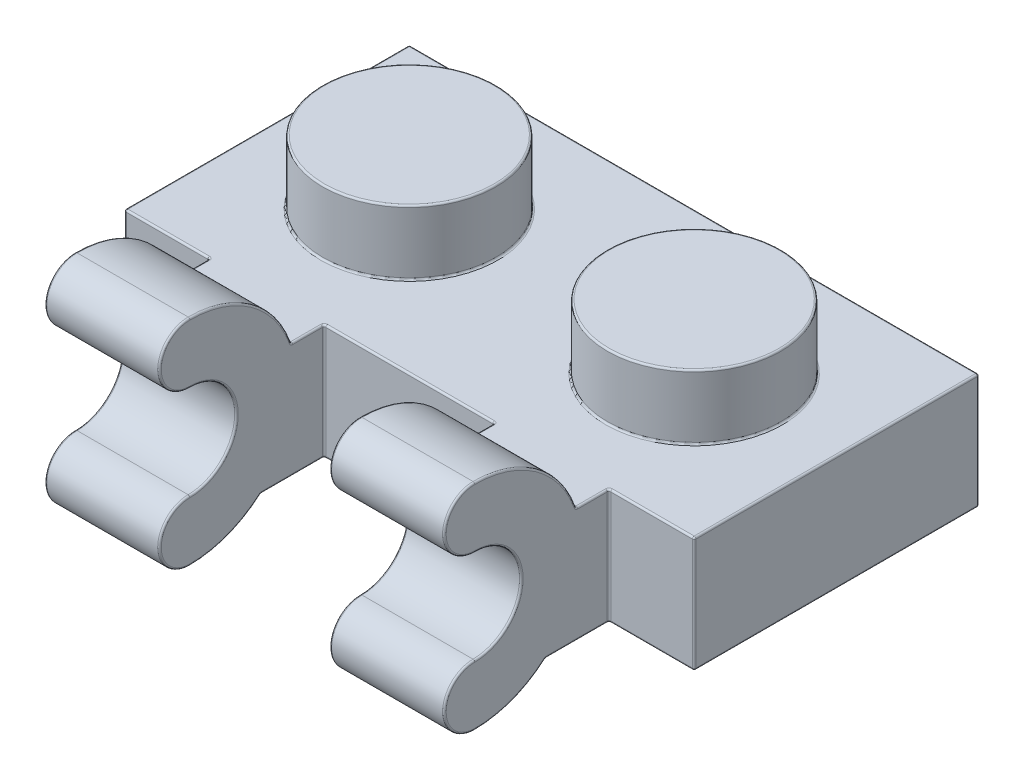
SolidWorks part; units mm, degrees
ref_plane "Front Plane" through (0, 0, 0) normal (0, 0, 1) x (1, 0, 0)
ref_plane "Top Plane" through (0, 0, 0) normal (0, 1, 0) x (1, 0, 0)
ref_plane "Right Plane" through (0, 0, 0) normal (1, 0, 0) x (0, 0, -1)
sketch "Sketch1" plane through (0, 0, 0) normal (0, 1, 0) x (1, 0, 0)
  line L1 (-3.98, 3.98) -> (3.98, 3.98)
  line L2 (-3.98, 3.98) -> (-3.98, -3.98)
  line L3 (-3.98, -3.98) -> (3.98, -3.98)
  line L4 (3.98, 3.98) -> (3.98, -3.98)
  line L5 (-3.98, 3.98) -> (3.98, -3.98) construction
  line L6 (-3.98, -3.98) -> (3.98, 3.98) construction
  point P0 (0, 0)
  dimension "D1" = 7.96
extrude "Extrude1" add sketch "Sketch1" along normal blind 3.22
sketch "Sketch2" plane through (0, 3.22, 0) normal (0, 1, 0) x (1, 0, 0)
  circle A0 centre (0, 0) radius 2.425
  dimension "D1" = 4.85
extrude "Extrude2" add sketch "Sketch2" along normal blind 1.8
pattern_linear "LPattern1" count 2 spacing 7.96 along (1, 0, 0) of "Extrude2", "Extrude1"
shell "Shell1" thickness 1.55
sketch "Sketch4" plane through (0, 1.67, 0) normal (0, -1, 0) x (1, 0, 0)
  line L0 (10.39, 2.43) -> (10.39, -2.43) construction
  line L1 (-2.43, 2.43) -> (10.39, 2.43) construction
  line L2 (-2.43, -2.43) -> (-2.43, 2.43) construction
  line L3 (10.39, -2.43) -> (-2.43, -2.43) construction
  line L4 (10.39, 2.43) -> (10.39, -2.43)
  line L5 (-2.43, 2.43) -> (10.39, 2.43)
  line L6 (-2.43, -2.43) -> (-2.43, 2.43)
  line L7 (10.39, -2.43) -> (-2.43, -2.43)
extrude "Extrude3" cut sketch "Sketch4" against normal blind 0.14
sketch "Sketch5" plane through (0, 1.81, 0) normal (0, -1, 0) x (1, 0, 0)
  line L0 (10.39, 2.43) -> (-2.43, 2.43) construction
  circle A0 centre (3.98, 0) radius 1.5
  circle A1 centre (3.98, 0) radius 0.64
  point P5 (3.98, 2.43)
  dimension "D1" = 3
  dimension "D2" = 0.86
extrude "Extrude4" add sketch "Sketch5" along normal up to surface (1.81 mm away) up to face at (3.98, 0, 0)
sketch "Sketch6" plane through (11.94, 0, 0) normal (1, 0, 0) x (0, 0, -1)
  line L0 (-3.98, 0) -> (-5.7457, 0)
  line L2 (-3.98, 3.22) -> (-3.98, 0) construction
  line L5 (-3.98, 0) -> (3.98, 0) construction
  line L7 (-3.98, 3.22) -> (-4.8911, 3.22)
  line L8 (-3.98, 3.22) -> (-3.98, 0)
  arc A0 (-4.8911, 3.22) -> (-7.73, 5.25) centre (-7.73, 2.25) ccw
  arc A1 (-7.73, 0.95) -> (-7.73, 3.55) centre (-7.73, 2.25) ccw
  arc A2 (-7.73, -0.75) -> (-5.7457, 0) centre (-7.73, 2.25) ccw
  arc A3 (-7.73, 0.95) -> (-7.73, -0.75) centre (-7.73, 0.1) ccw
  arc A4 (-7.73, 5.25) -> (-7.73, 3.55) centre (-7.73, 4.4) ccw
  dimension "D1" = 6
  dimension "D2" = 1.7
  dimension "D3" = 3.75
  dimension "D4" = 2.25
sketch "Sketch7" plane through (0, 0, 0) normal (1, 0, 0) x (0, 0, -1)
  line L0 (-3.98, 3.22) -> (-3.98, 0) construction
  line L1 (-3.98, 3.22) -> (-4.8911, 3.22) construction
  line L2 (-3.98, 0) -> (-5.7457, 0) construction
  line L3 (-3.98, 3.22) -> (-3.98, 0)
  line L4 (-3.98, 3.22) -> (-4.8911, 3.22)
  line L5 (-3.98, 0) -> (-5.7457, 0)
  arc A0 (-4.8911, 3.22) -> (-7.73, 5.25) centre (-7.73, 2.25) ccw construction
  arc A1 (-7.73, 5.25) -> (-7.73, 3.55) centre (-7.73, 4.4) ccw construction
  arc A2 (-7.73, 0.95) -> (-7.73, 3.55) centre (-7.73, 2.25) ccw construction
  arc A3 (-7.73, 0.95) -> (-7.73, -0.75) centre (-7.73, 0.1) ccw construction
  arc A4 (-7.73, -0.75) -> (-5.7457, 0) centre (-7.73, 2.25) ccw construction
  arc A5 (-4.8911, 3.22) -> (-7.73, 5.25) centre (-7.73, 2.25) ccw
  arc A6 (-7.73, 5.25) -> (-7.73, 3.55) centre (-7.73, 4.4) ccw
  arc A7 (-7.73, 0.95) -> (-7.73, 3.55) centre (-7.73, 2.25) ccw
  arc A8 (-7.73, 0.95) -> (-7.73, -0.75) centre (-7.73, 0.1) ccw
  arc A9 (-7.73, -0.75) -> (-5.7457, 0) centre (-7.73, 2.25) ccw
extrude "Extrude6" add sketch "Sketch7" along normal blind 1.6 and the other way blind 1.6
pattern_linear "LPattern2" count 2 spacing 7.96 along (1, 0, 0) of "Extrude6"
fillet "Fillet1" radius 0.05 76 edges at (-3.98, 3.22, 0) (9.56, 4.6903, 5.985) (9.56, 4.4, 8.58) (9.56, 2.25, 6.43) (9.56, 0.1, 8.58) (9.56, -0.5562, 6.6693) (9.56, 0, 4.8628) (9.56, 1.61, 3.98) (0, 3.22, 2.425) (0, 5.02, 2.425) (11.94, 0, 0) (11.94, 1.61, 3.98) (11.94, 1.61, -3.98) (11.94, 3.22, 0) (7.96, 3.22, 2.425) (7.96, 5.02, 2.425) (3.98, 0, -2.43) (10.39, 0.905, -2.43) (-2.43, 0, 0) (-2.43, 0.905, -2.43) (3.98, 0, 2.43) (-2.43, 0.905, 2.43) (0, 3.47, 0.875) (10.39, 0, 0) (10.39, 0.905, 2.43) (7.96, 3.47, 0.875) (0, 1.81, 0.875) (7.96, 1.81, 0.875) (3.98, 1.81, 2.43) (10.39, 1.81, 0) (-3.98, 0, 0) (3.98, 1.81, -2.43) (-2.43, 1.81, 0) (3.98, 0, -3.98) (3.98, 1.81, 1.5) (3.98, 1.81, -0.64) (3.98, 0, 1.5) (3.98, 0, 0.64) (3.98, 3.22, -3.98) (0, 3.22, 4.8911) (0, 0, 5.7457) (-1.6, -0.5562, 6.6693) (-3.98, 1.61, 3.98) (-1.6, 0.1, 8.58) (-1.6, 2.25, 6.43) (-1.6, 4.4, 8.58) (-3.98, 1.61, -3.98) (-1.6, 4.6903, 5.985) (1.6, 4.6903, 5.985) (1.6, 4.4, 8.58) (1.6, 2.25, 6.43) (1.6, 0.1, 8.58) (1.6, -0.5562, 6.6693) (7.96, 3.22, 4.8911) (6.36, 3.22, 4.4356) (6.36, 1.61, 3.98) (6.36, 0, 4.8628) (7.96, 0, 5.7457) (6.36, -0.5562, 6.6693) (6.36, 0.1, 8.58) (6.36, 2.25, 6.43) (6.36, 4.4, 8.58) (6.36, 4.6903, 5.985) (9.56, 3.22, 4.4356)
